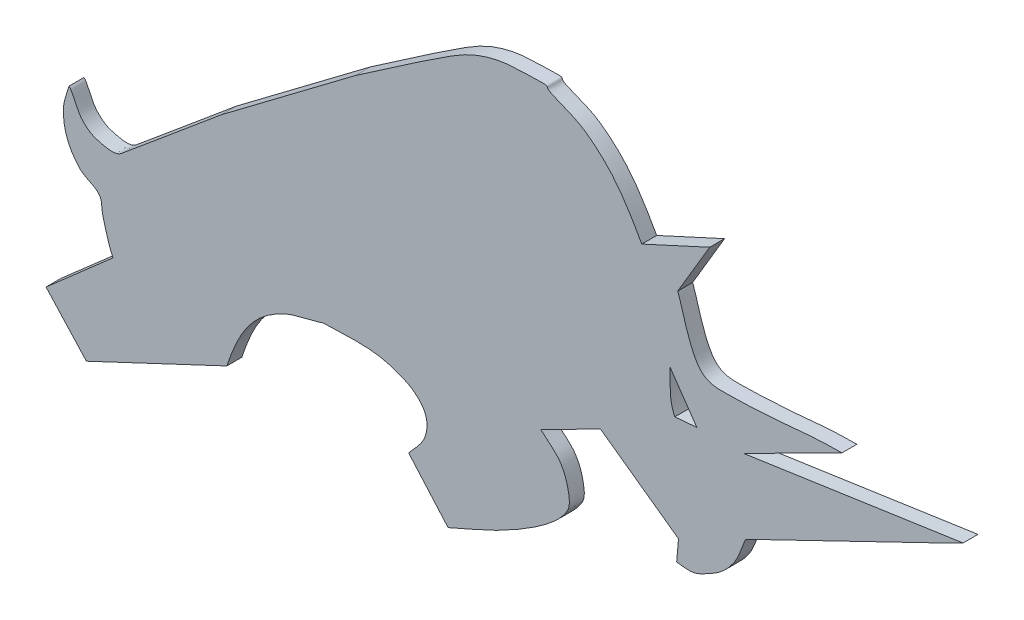
SolidWorks part; units mm, degrees
ref_plane "Front Plane" through (0, 0, 0) normal (0, 0, 1) x (1, 0, 0)
ref_plane "Top Plane" through (0, 0, 0) normal (0, 1, 0) x (1, 0, 0)
ref_plane "Right Plane" through (0, 0, 0) normal (1, 0, 0) x (0, 0, -1)
sketch "Sketch1" plane through (0, 0, 0) normal (0, 0, 1) x (1, 0, 0)
  line L0 (172.5, 282) -> (862.5, 282) construction
  line L1 (6.3438, 10.4063) -> (10.9063, 13.8438)
  line L2 (20.6562, 13.75) -> (22.9688, 14.8125)
  line L3 (22.9688, 14.8125) -> (21.875, 12.9688)
  line L4 (27.4688, 11) -> (24.125, 9.3125)
  line L5 (24.125, 9.3125) -> (31.5938, 10.4063)
  line L6 (31.5938, 10.4063) -> (30.8438, 10.0313)
  line L7 (30.8438, 10.0313) -> (24.1875, 6.8125)
  line L8 (21.8438, 4.9688) -> (21.9063, 5.6875)
  line L9 (21.9063, 5.6875) -> (19.25, 7.5938)
  line L10 (19.25, 7.5938) -> (17.2188, 6.5625)
  line L11 (14.0625, 2.0938) -> (12.7188, 3.625)
  line L12 (6.5312, 3.0938) -> (1.75, 0.8438)
  line L13 (1.75, 0.8438) -> (0.375, 2.3438)
  line L14 (0.375, 2.3438) -> (2.6562, 4.3438)
  line L15 (21.625, 10.5938) -> (22.5312, 9.2813)
  line L16 (22.5312, 9.2813) -> (21.7813, 9.2188)
  line L17 (6.3438, 10.4063) -> (10.9063, 13.8438)
  line L18 (20.6562, 13.75) -> (22.9688, 14.8125)
  line L19 (22.9688, 14.8125) -> (21.875, 12.9688)
  line L20 (27.4688, 11) -> (24.125, 9.3125)
  line L21 (24.125, 9.3125) -> (31.5938, 10.4063)
  line L22 (31.5938, 10.4063) -> (30.8438, 10.0313)
  line L23 (30.8438, 10.0313) -> (24.1875, 6.8125)
  line L24 (21.8438, 4.9688) -> (21.9063, 5.6875)
  line L25 (21.9063, 5.6875) -> (19.25, 7.5938)
  line L26 (19.25, 7.5938) -> (17.2188, 6.5625)
  line L27 (14.0625, 2.0938) -> (12.7188, 3.625)
  line L28 (6.5312, 3.0938) -> (1.75, 0.8438)
  line L29 (1.75, 0.8438) -> (0.375, 2.3438)
  line L30 (0.375, 2.3438) -> (2.6562, 4.3438)
  line L31 (21.625, 10.5938) -> (22.5312, 9.2813)
  line L32 (22.5312, 9.2813) -> (21.7813, 9.2188)
  line L33 (21.7813, 9.2188) -> (21.625, 10.5938)
  spline S0 degree 3 poles (1.1562, 8.6562) (1.1771, 8.6354) (1.2039, 8.6192) (1.2188, 8.5938) (1.3503, 8.3683) (1.4249, 8.1053) (1.5938, 7.9063) (1.7246, 7.752) (1.8996, 7.6193) (2.0938, 7.5625) (2.3637, 7.4835) (2.721, 7.383) (2.9375, 7.5625) (4.0763, 8.5064) (5.2083, 9.4583) (6.3438, 10.4063) knots 0 0 0 0 1 1 1 2 2 2 3 3 3 4 4 4 5 5 5 5
  spline S1 degree 3 poles (10.9063, 13.8438) (12, 14.5833) (13.0729, 15.3547) (14.1875, 16.0625) (14.5021, 16.2623) (14.835, 16.4415) (15.1875, 16.5625) (15.5392, 16.6832) (15.9097, 16.7666) (16.2812, 16.7812) (17.9353, 16.8465) (17.1597, 16.8377) (17.625, 16.625) (17.9684, 16.468) (18.3398, 16.3622) (18.6562, 16.1562) (19.0028, 15.9307) (19.3168, 15.6509) (19.5938, 15.3438) (20.0213, 14.8696) (20.3432, 14.3065) (20.6562, 13.75) knots 0 0 0 0 1 1 1 2 2 2 3 3 3 4 4 4 5 5 5 6 6 6 7 7 7 7
  spline S2 degree 3 poles (21.875, 12.9688) (21.8854, 12.9479) (21.8987, 12.9283) (21.9063, 12.9063) (22.0655, 12.4385) (22.1711, 11.9501) (22.375, 11.5) (22.4765, 11.2761) (22.6037, 11.036) (22.8125, 10.9063) (23.019, 10.7779) (23.2881, 10.7773) (23.5312, 10.7813) (25.6087, 10.8148) (25.9788, 11) (27.4688, 11) knots 0 0 0 0 1 1 1 2 2 2 3 3 3 4 4 4 5 5 5 5
  spline S3 degree 3 poles (24.1875, 6.8125) (24.0521, 6.5104) (23.97, 6.1782) (23.7812, 5.9063) (23.609, 5.6581) (23.3845, 5.4359) (23.125, 5.2813) (22.4276, 4.8655) (22.3841, 4.9147) (21.8438, 4.9688) knots 0 0 0 0 1 1 1 2 2 2 3 3 3 3
  spline S4 degree 3 poles (17.2188, 6.5625) (17.4375, 6.3542) (17.7022, 6.1852) (17.875, 5.9375) (18.0222, 5.7265) (18.1081, 5.4715) (18.1562, 5.2188) (18.1933, 5.0241) (18.2229, 4.7973) (18.125, 4.625) (17.9467, 4.3111) (17.6623, 4.0623) (17.375, 3.8438) (16.9171, 3.4955) (16.4149, 3.2062) (15.9062, 2.9375) (15.3086, 2.6218) (14.6771, 2.375) (14.0625, 2.0938) knots 0 0 0 0 1 1 1 2 2 2 3 3 3 4 4 4 5 5 5 6 6 6 6
  spline S5 degree 3 poles (12.7188, 3.625) (12.8854, 3.8333) (13.0945, 4.0139) (13.2188, 4.25) (13.3082, 4.42) (13.3554, 4.6208) (13.3438, 4.8125) (13.3336, 4.9805) (13.2631, 5.1512) (13.1562, 5.2813) (13.0147, 5.4535) (12.8282, 5.5959) (12.625, 5.6875) (12.2885, 5.8393) (11.9295, 5.9597) (11.5625, 6) (10.9723, 6.0649) (10.3749, 6.0101) (9.7812, 6) (9.758, 5.9996) (9.7411, 5.9754) (9.7188, 5.9688) (9.324, 5.8503) (8.9085, 5.7908) (8.5312, 5.625) (7.363, 5.1117) (6.9119, 4.2357) (6.5312, 3.0938) knots 0 0 0 0 1 1 1 2 2 2 3 3 3 4 4 4 5 5 5 6 6 6 7 7 7 8 8 8 9 9 9 9
  spline S6 degree 3 poles (2.6562, 4.3438) (2.4898, 4.6767) (2.4129, 5.0478) (2.3125, 5.4063) (2.2607, 5.5912) (2.3057, 5.8174) (2.1875, 5.9688) (2.0256, 6.1759) (1.7145, 6.2177) (1.5312, 6.4063) (1.3419, 6.601) (1.1891, 6.8394) (1.0938, 7.0938) (0.9975, 7.3503) (0.9578, 7.6324) (0.9688, 7.9063) (0.979, 8.1637) (1.0938, 8.4063) (1.1562, 8.6562) knots 0 0 0 0 1 1 1 2 2 2 3 3 3 4 4 4 5 5 5 6 6 6 6
  spline S7 degree 3 poles (21.7813, 9.2188) (21.5708, 9.6396) (21.625, 10.1348) (21.625, 10.5938) knots 0 0 0 0 1 1 1 1
  spline S8 degree 3 poles (1.1562, 8.6562) (1.1771, 8.6354) (1.2039, 8.6192) (1.2188, 8.5938) (1.3503, 8.3683) (1.4249, 8.1053) (1.5938, 7.9063) (1.7246, 7.752) (1.8996, 7.6193) (2.0938, 7.5625) (2.3637, 7.4835) (2.721, 7.383) (2.9375, 7.5625) (4.0763, 8.5064) (5.2083, 9.4583) (6.3438, 10.4063) knots 0 0 0 0 1 1 1 2 2 2 3 3 3 4 4 4 5 5 5 5
  spline S9 degree 3 poles (10.9063, 13.8438) (12, 14.5833) (13.0729, 15.3547) (14.1875, 16.0625) (14.5021, 16.2623) (14.835, 16.4415) (15.1875, 16.5625) (15.5392, 16.6832) (15.9097, 16.7666) (16.2812, 16.7812) (17.9353, 16.8465) (17.1597, 16.8377) (17.625, 16.625) (17.9684, 16.468) (18.3398, 16.3622) (18.6562, 16.1562) (19.0028, 15.9307) (19.3168, 15.6509) (19.5938, 15.3438) (20.0213, 14.8696) (20.3432, 14.3065) (20.6562, 13.75) knots 0 0 0 0 1 1 1 2 2 2 3 3 3 4 4 4 5 5 5 6 6 6 7 7 7 7
  spline S10 degree 3 poles (21.875, 12.9688) (21.8854, 12.9479) (21.8987, 12.9283) (21.9063, 12.9063) (22.0655, 12.4385) (22.1711, 11.9501) (22.375, 11.5) (22.4765, 11.2761) (22.6037, 11.036) (22.8125, 10.9063) (23.019, 10.7779) (23.2881, 10.7773) (23.5312, 10.7813) (25.6087, 10.8148) (25.9788, 11) (27.4688, 11) knots 0 0 0 0 1 1 1 2 2 2 3 3 3 4 4 4 5 5 5 5
  spline S11 degree 3 poles (24.1875, 6.8125) (24.0521, 6.5104) (23.97, 6.1782) (23.7812, 5.9063) (23.609, 5.6581) (23.3845, 5.4359) (23.125, 5.2813) (22.4276, 4.8655) (22.3841, 4.9147) (21.8438, 4.9688) knots 0 0 0 0 1 1 1 2 2 2 3 3 3 3
  spline S12 degree 3 poles (17.2188, 6.5625) (17.4375, 6.3542) (17.7022, 6.1852) (17.875, 5.9375) (18.0222, 5.7265) (18.1081, 5.4715) (18.1562, 5.2188) (18.1933, 5.0241) (18.2229, 4.7973) (18.125, 4.625) (17.9467, 4.3111) (17.6623, 4.0623) (17.375, 3.8438) (16.9171, 3.4955) (16.4149, 3.2062) (15.9062, 2.9375) (15.3086, 2.6218) (14.6771, 2.375) (14.0625, 2.0938) knots 0 0 0 0 1 1 1 2 2 2 3 3 3 4 4 4 5 5 5 6 6 6 6
  spline S13 degree 3 poles (12.7188, 3.625) (12.8854, 3.8333) (13.0945, 4.0139) (13.2188, 4.25) (13.3082, 4.42) (13.3554, 4.6208) (13.3438, 4.8125) (13.3336, 4.9805) (13.2631, 5.1512) (13.1562, 5.2813) (13.0147, 5.4535) (12.8282, 5.5959) (12.625, 5.6875) (12.2885, 5.8393) (11.9295, 5.9597) (11.5625, 6) (10.9723, 6.0649) (10.3749, 6.0101) (9.7812, 6) (9.758, 5.9996) (9.7411, 5.9754) (9.7188, 5.9688) (9.324, 5.8503) (8.9085, 5.7908) (8.5312, 5.625) (7.363, 5.1117) (6.9119, 4.2357) (6.5312, 3.0938) knots 0 0 0 0 1 1 1 2 2 2 3 3 3 4 4 4 5 5 5 6 6 6 7 7 7 8 8 8 9 9 9 9
  spline S14 degree 3 poles (2.6562, 4.3438) (2.4898, 4.6767) (2.4129, 5.0478) (2.3125, 5.4063) (2.2607, 5.5912) (2.3057, 5.8174) (2.1875, 5.9688) (2.0256, 6.1759) (1.7145, 6.2177) (1.5312, 6.4063) (1.3419, 6.601) (1.1891, 6.8394) (1.0938, 7.0938) (0.9975, 7.3503) (0.9578, 7.6324) (0.9688, 7.9063) (0.979, 8.1637) (1.0938, 8.4063) (1.1562, 8.6562) knots 0 0 0 0 1 1 1 2 2 2 3 3 3 4 4 4 5 5 5 6 6 6 6
extrude "Boss-Extrude2" add sketch "Sketch1" along normal blind 0.508 contours S6 L14 L13 L12 S5 L11 S4 L10 L9 L8 S3 L7 L6 L5 L4 S2 L3 L2 S1 L1 S0 L16 S7 L15
